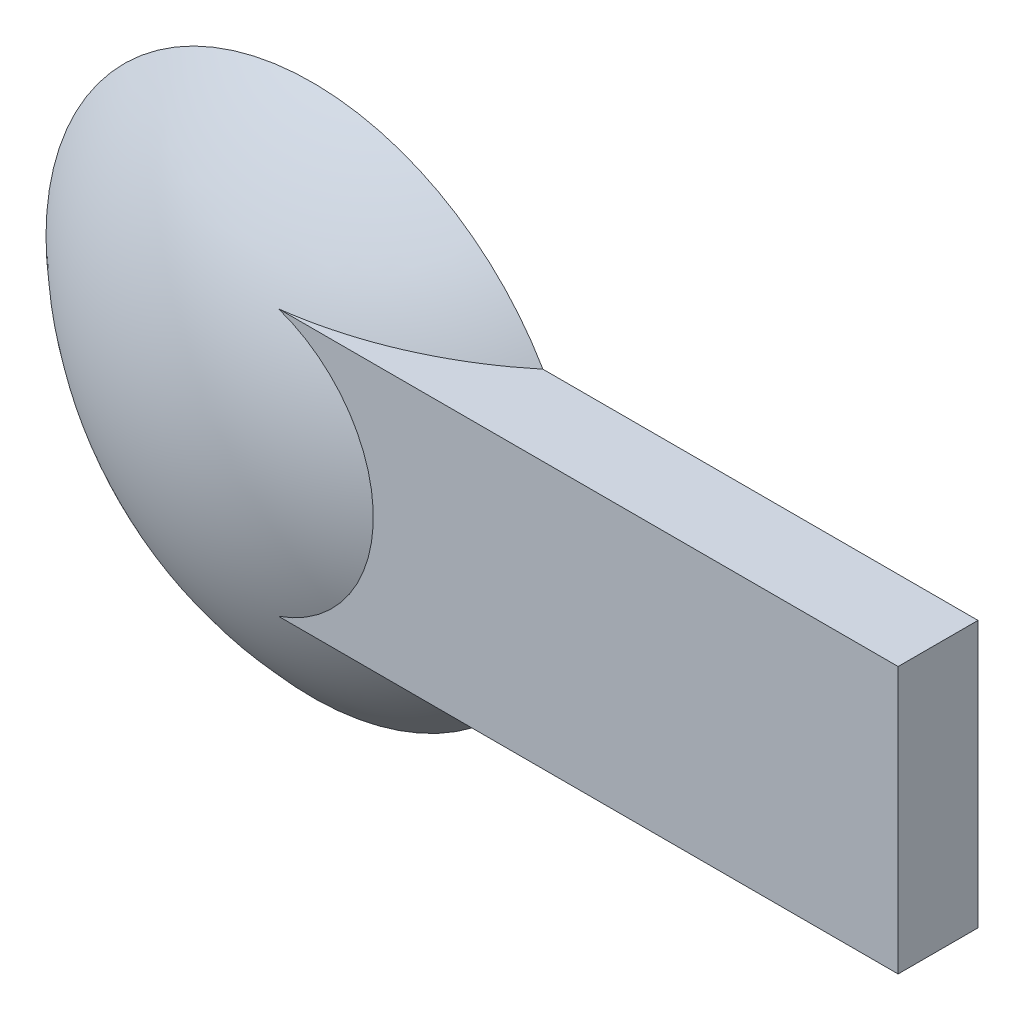
SolidWorks part; units mm, degrees
ref_plane "Plan de face" through (0, 0, 0) normal (0, 0, 1) x (1, 0, 0)
ref_plane "Plan de dessus" through (0, 0, 0) normal (0, 1, 0) x (1, 0, 0)
ref_plane "Plan de droite" through (0, 0, 0) normal (1, 0, 0) x (0, 0, -1)
sketch "Esquisse1" plane through (0, 0, 0) normal (0, 1, 0) x (1, 0, 0)
  line L0 (0, 0) -> (0, -4)
  line L1 (0, 0) -> (-10, 0)
  line L2 (0, -4) -> (-20.1028, -4) construction
  arc A0 (-10, 0) -> (0, -4) centre (0, 10.5) ccw
  dimension "D1" = 10
  dimension "D2" = 4
revolve "Révolution1" add sketch "Esquisse1" angle 360 about L0
ref_plane "Plan1" through (25, 0, 0) normal (1, 0, 0) x (0, 0, -1)
sketch "Esquisse2" plane through (25, 0, -10) normal (-1, 0, 0) x (0, 0, 1)
  line L0 (10, 10) -> (10, -10) construction
  line L1 (13, 5) -> (10, 5)
  line L2 (13, 5) -> (13, -5)
  line L3 (13, -5) -> (10, -5)
  line L4 (10, 5) -> (10, -5)
  dimension "D1" = 5
  dimension "D2" = 10
  dimension "D3" = 3
extrude "Boss.-Extru.1" add sketch "Esquisse2" along normal up to next
